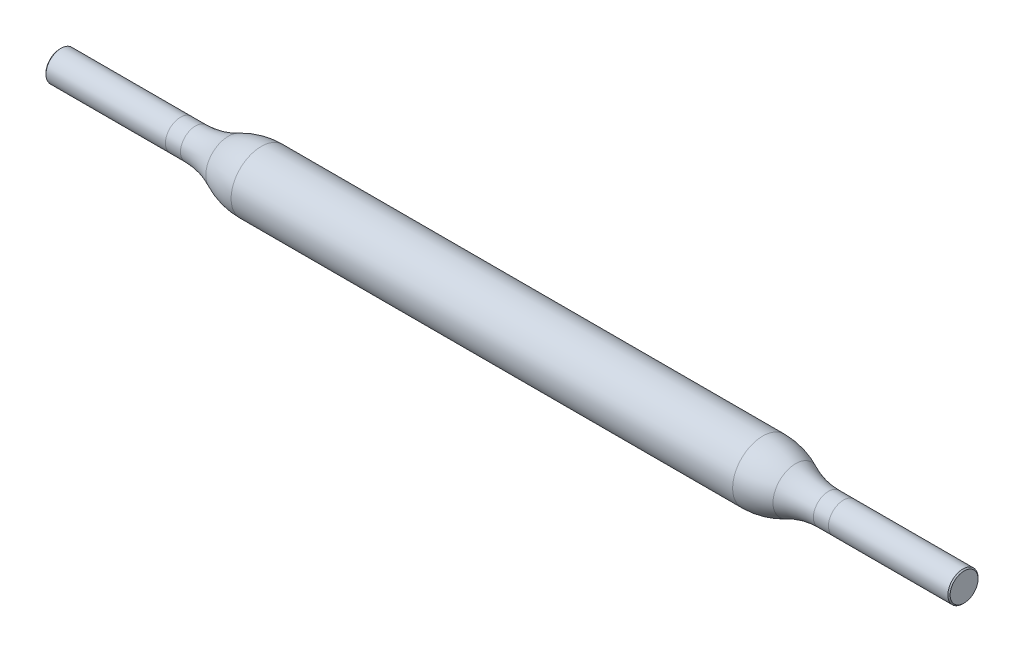
SolidWorks part; units mm, degrees
ref_plane "Front Plane" through (0, 0, 0) normal (0, 0, 1) x (1, 0, 0)
ref_plane "Top Plane" through (0, 0, 0) normal (0, 1, 0) x (1, 0, 0)
ref_plane "Right Plane" through (0, 0, 0) normal (1, 0, 0) x (0, 0, -1)
sketch "Sketch1" plane through (0, 0, 0) normal (0, 0, 1) x (1, 0, 0)
  line L0 (-30, -3.052) -> (30, -3.052)
  line L1 (30, -3.052) -> (30, -2.052)
  line L2 (-30, -3.052) -> (-30, -2.052)
  line L3 (-30, -2.052) -> (-21, -2.052)
  line L4 (-16.6411, -1.052) -> (16.6411, -1.052)
  line L5 (30, -2.052) -> (21, -2.052)
  arc A0 (-21, -2.052) -> (-18.8206, -1.552) centre (-21, 2.948) ccw
  arc A1 (18.8206, -1.552) -> (21, -2.052) centre (21, 2.948) ccw
  arc A2 (16.6411, -1.052) -> (18.8206, -1.552) centre (16.6411, -6.052) cw
  arc A3 (-16.6411, -1.052) -> (-18.8206, -1.552) centre (-16.6411, -6.052) ccw
  point P2 (0, -3.052)
  point P9 (0, -1.052)
  point P17 (-18, -1.052)
  dimension "D6" = 3
  dimension "D7" = 5
  dimension "D1" = 60
  dimension "D2" = 1
  dimension "D3" = 9
  dimension "D4" = 9
  dimension "D5" = 2
revolve "Revolve1" add sketch "Sketch1" angle 360 about L0
sketch "Sketch2" plane through (0, 0, 0) normal (0, 0, 1) x (1, 0, 0)
  line L0 (-22, 0.6658) -> (-22, -6.9638)
  line L1 (22, 0.6658) -> (22, -6.9638)
  dimension "D1" = 8
  dimension "D2" = 8
split line "Split Line1"
chamfer "Chamfer1" distance 0.075 angle 45 2 edges at (-30, -3.052, 1) (30, -3.052, 1)
